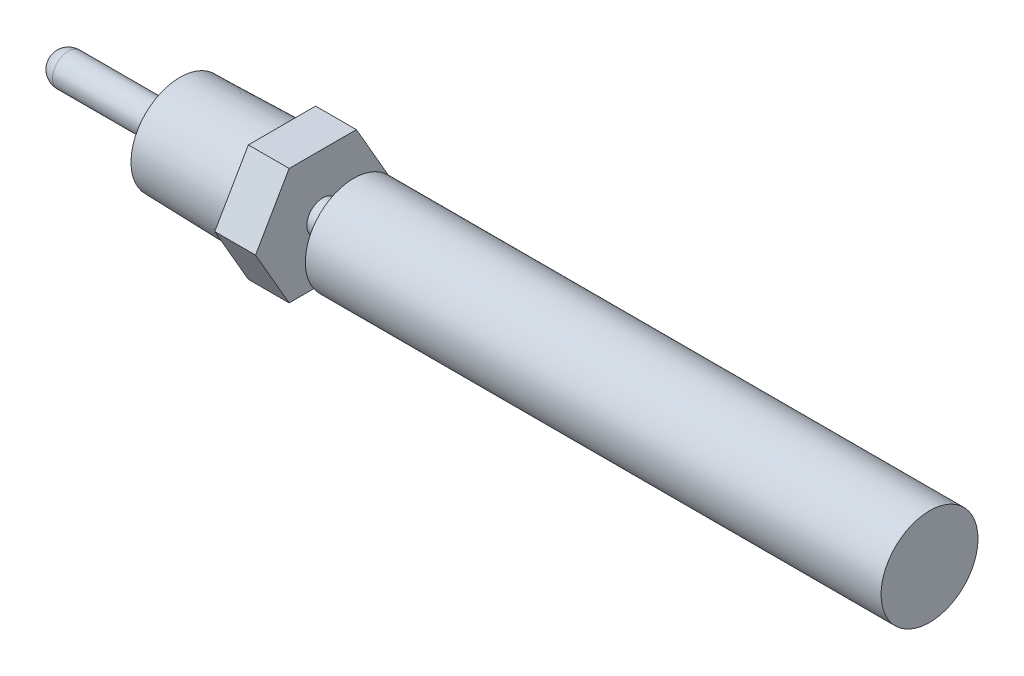
SolidWorks part; units mm, degrees
material "AISI 304"
ref_plane "Front Plane" through (0, 0, 0) normal (0, 0, 1) x (1, 0, 0)
ref_plane "Top Plane" through (0, 0, 0) normal (0, 1, 0) x (1, 0, 0)
ref_plane "Right Plane" through (0, 0, 0) normal (1, 0, 0) x (0, 0, -1)
sketch "Sketch1" plane through (0, 0, 0) normal (0, 0, 1) x (1, 0, 0)
  line L0 (0, 0) -> (-60.2836, 0) construction
  line L1 (-60.2836, 0) -> (55.991, 0) construction
  line L3 (0, 1.5875) -> (11.1125, 1.5875)
  line L4 (11.1125, 1.5875) -> (11.1125, 4.8828)
  line L5 (11.1125, 4.8828) -> (21.2725, 5.1435)
  line L6 (21.2725, 5.1435) -> (21.2725, 6.6992)
  line L7 (21.2725, 6.6992) -> (25.3365, 6.6992)
  line L8 (25.3365, 6.6992) -> (25.3365, 1.5875)
  line L9 (25.3365, 1.5875) -> (28.4269, 1.5875)
  line L10 (28.4269, 1.5875) -> (28.4269, 4.826)
  line L11 (85.7885, 4.826) -> (28.4269, 4.826)
  line L12 (-1.5875, 0) -> (-1.5875, 7.1342) construction
  line L13 (11.1125, 4.8828) -> (31.6688, 4.8828) construction
  line L14 (85.7885, 4.826) -> (85.7885, 0)
  line L15 (85.7885, 0) -> (0, 0)
  line L16 (0, 0) -> (-1.5875, 0)
  arc A0 (0, 1.5875) -> (-1.5875, 0) centre (0, 0) ccw
  dimension "D1" = 3.175
  dimension "D2" = 12.7
  dimension "D3" = 14.224
  dimension "D4" = 1.47
  dimension "D5" = 10.16
  dimension "D6" = 5.1435
  dimension "D7" = 1.5875
  dimension "D8" = 4.826
  dimension "D9" = 60.452
revolve "Revolve1" add sketch "Sketch1" angle 360 about L15
sketch "Sketch2" plane through (25.3365, 0, 0) normal (1, 0, 0) x (0, 0, -1)
  line L1 (6.6992, 0) -> (3.3496, 5.8017)
  line L2 (3.3496, 5.8017) -> (-3.3496, 5.8017)
  line L3 (-3.3496, 5.8017) -> (-6.6992, 0)
  line L4 (-6.6992, 0) -> (-3.3496, -5.8017)
  line L5 (-3.3496, -5.8017) -> (3.3496, -5.8017)
  line L6 (3.3496, -5.8017) -> (6.6992, 0)
  circle A0 centre (0, 0) radius 5.8017 construction
  circle A1 centre (0, 0) radius 9.1341
extrude "Cut-Extrude1" cut sketch "Sketch2" against normal up to next
